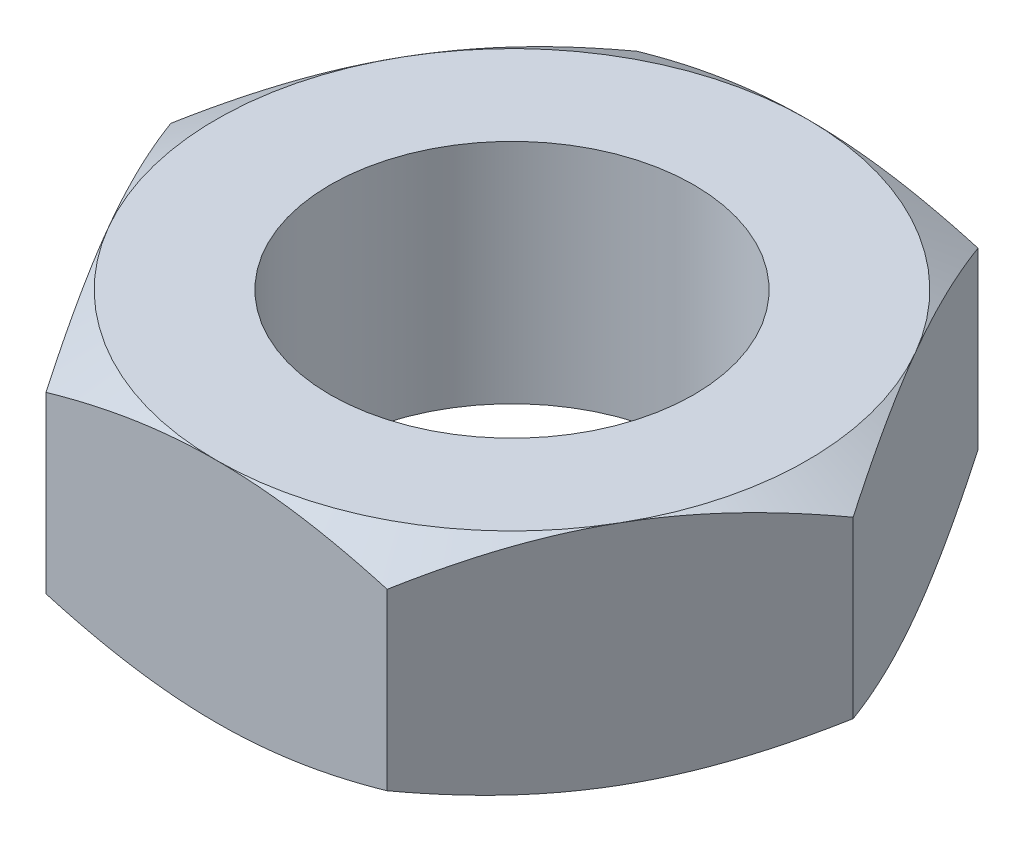
SolidWorks part; units mm, degrees
ref_plane "Plan1" through (0, 0, 0) normal (0, 0, 1) x (1, 0, 0)
ref_plane "Plan2" through (0, 0, 0) normal (0, 1, 0) x (1, 0, 0)
ref_plane "Plan3" through (0, 0, 0) normal (1, 0, 0) x (0, 0, -1)
sketch "Esquisse1" plane through (0, 0, 0) normal (0, 0, 1) x (1, 0, 0)
  line L1 (4, 5) -> (6.5, 5)
  line L2 (6.5, 5) -> (9.1924, 3.4455)
  line L3 (9.1924, 3.4455) -> (9.1924, 1.5545)
  line L4 (9.1924, 1.5545) -> (6.5, 0)
  line L5 (6.5, 0) -> (4, 0)
  line L6 (0, 2.4) -> (0, 0) construction
  line L7 (4, 5) -> (4, 0)
  line L8 (-6.5, 0) -> (6.5, 0) construction
  line L9 (0, 0) -> (8, 0) construction
  line L10 (-4, 0) -> (4, 0) construction
  dimension "D1" = 9.1924
  dimension "Hauteur" = 5
  dimension "D2" = 30
  dimension "D4" = 6.5
  dimension "D5" = 30
  dimension "D6" = 4
  dimension "Cote sur plats" = 13
  dimension "Diamètre nominal" = 8
revolve "Base-Révolution" add sketch "Esquisse1" angle 360 about L6
sketch "Esquisse2" plane through (0, 0, 0) normal (0, 1, 0) x (1, 0, 0)
  line L0 (0, 2.4733) -> (0, -2.457) construction
  line L1 (0, 0) -> (1.6745, -2.9003) construction
  line L2 (-3.7528, -6.5) -> (3.7528, -6.5)
  line L3 (0, 0) -> (2.3797, -1.3739) construction
  line L4 (3.7528, -6.5) -> (7.5056, 0)
  line L5 (0, 0) -> (2.9763, 0) construction
  line L6 (3.7528, 6.5) -> (7.5056, 0)
  line L7 (-3.7528, 6.5) -> (3.7528, 6.5)
  line L8 (-3.7528, 6.5) -> (-7.5056, 0)
  line L9 (-3.7528, -6.5) -> (-7.5056, 0)
  circle A1 centre (0, 0) radius 6.5 construction
  point P14 (0, 6.5)
  point P16 (0, -6.5)
  dimension "D1" = 30
  dimension "D2" = 30
extrude "Enlèv. mat.-Extru.1" cut sketch "Esquisse2" along normal blind 5 flip side to cut
equation "\"D4@Esquisse1\" = \"Cote sur plats@Esquisse1\"/2"
equation "\"D1@Esquisse1\" =(\"D4@Esquisse1\"*sqr(2)*2)/2"
equation "\"D1@Enlèv. mat.-Extru.1\" = \"Hauteur@Esquisse1\""
equation "\"D6@Esquisse1\" = \"Diamètre nominal@Esquisse1\"/2"
